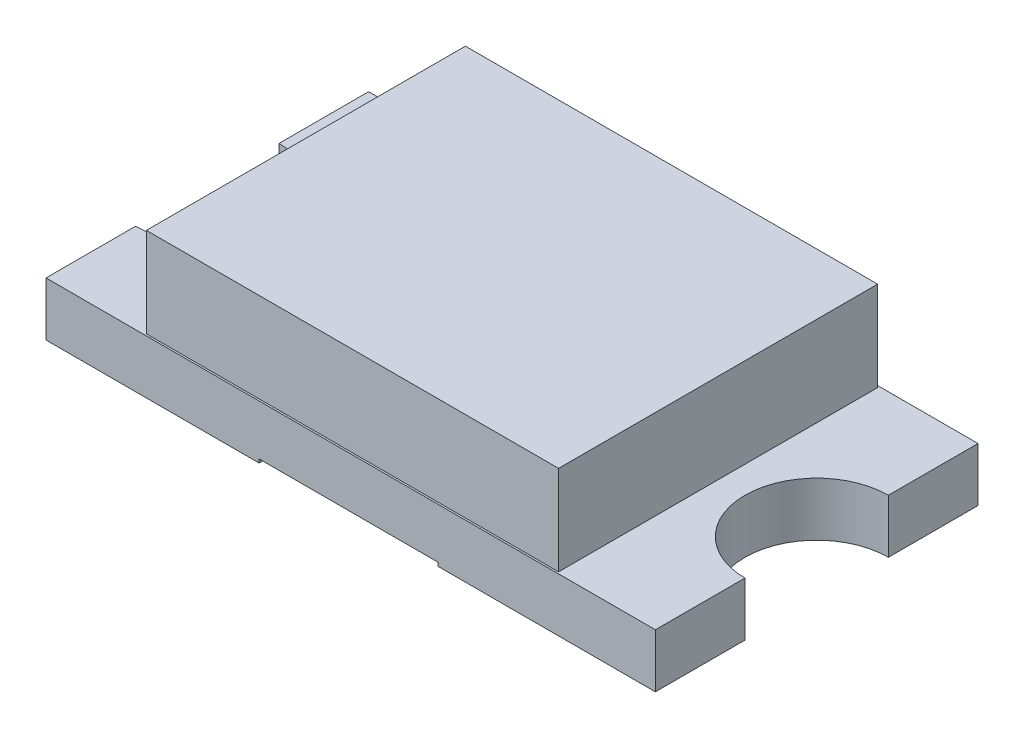
SolidWorks part; units mm, degrees
ref_plane "Front Plane" through (0, 0, 0) normal (0, 0, 1) x (1, 0, 0)
ref_plane "Top Plane" through (0, 0, 0) normal (0, 1, 0) x (1, 0, 0)
ref_plane "Right Plane" through (0, 0, 0) normal (1, 0, 0) x (0, 0, -1)
sketch "Sketch1" plane through (0, 0, 0) normal (0, 1, 0) x (1, 0, 0)
  line L0 (0, 0.45) -> (0, -0.45) construction
  line L1 (-0.85, -0.45) -> (0.85, -0.45)
  line L2 (-0.85, -0.45) -> (-0.85, 0.45)
  line L3 (-0.85, 0.45) -> (0.85, 0.45)
  line L4 (0.85, -0.45) -> (0.85, 0.45)
  line L5 (0, 0) -> (0.1875, 0) construction
  dimension "D1" = 0.9
  dimension "D2" = 1.7
extrude "Boss-Extrude1" add sketch "Sketch1" along normal blind 0.15
sketch "Sketch2" plane through (0, 0.15, 0) normal (0, 1, 0) x (1, 0, 0)
  line L0 (-0.85, 0.45) -> (-0.85, -0.45) construction
  line L1 (0.85, -0.45) -> (0.85, 0.45) construction
  circle A0 centre (-0.85, 0) radius 0.2
  circle A1 centre (0.85, 0) radius 0.2
  dimension "D1" = 0.4
extrude "Cut-Extrude1" cut sketch "Sketch2" against normal through all
sketch "Sketch3" plane through (0, 0.15, 0) normal (0, 1, 0) x (1, 0, 0)
  line L0 (0, -0.0817) -> (0, 0.1379) construction
  line L1 (-0.575, -0.445) -> (0.575, -0.445)
  line L2 (-0.575, -0.445) -> (-0.575, 0.445)
  line L3 (-0.575, 0.445) -> (0.575, 0.445)
  line L4 (0.575, -0.445) -> (0.575, 0.445)
  line L8 (-0.0877, 0) -> (0.1161, 0) construction
  dimension "D1" = 1.15
  dimension "D2" = 0.89
extrude "Boss-Extrude3" add sketch "Sketch3" along normal blind 0.25
sketch "Sketch4" plane through (0, 0, 0) normal (0, -1, 0) x (1, 0, 0)
  line L0 (-0.85, 0.45) -> (0.85, 0.45) construction
  line L1 (-0.2556, 0.45) -> (0.2437, 0.45)
  line L2 (-0.2556, 0.45) -> (-0.2556, -0.45)
  line L3 (-0.2556, -0.45) -> (0.2437, -0.45)
  line L4 (0.2437, 0.45) -> (0.2437, -0.45)
  line L5 (0.85, -0.45) -> (-0.85, -0.45) construction
extrude "Cut-Extrude2" cut sketch "Sketch4" against normal blind 0.01
